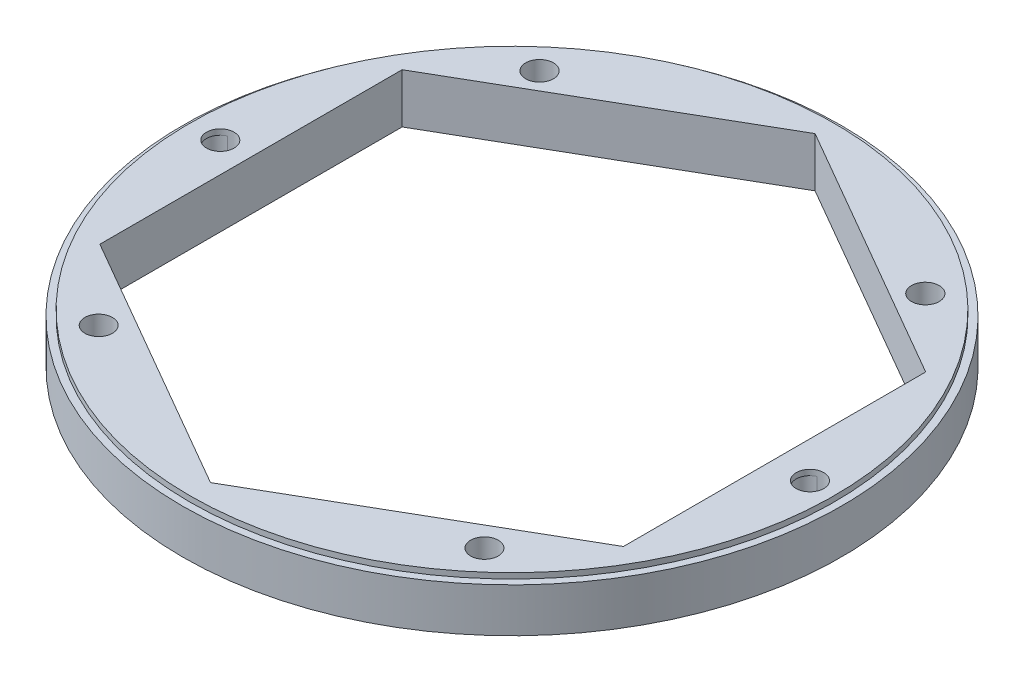
SolidWorks part; units mm, degrees
ref_plane "Front Plane" through (0, 0, 0) normal (0, 0, 1) x (1, 0, 0)
ref_plane "Top Plane" through (0, 0, 0) normal (0, 1, 0) x (1, 0, 0)
ref_plane "Right Plane" through (0, 0, 0) normal (1, 0, 0) x (0, 0, -1)
sketch "Sketch1" plane through (0, 0, 0) normal (0, 1, 0) x (1, 0, 0)
  circle A0 centre (0, 0) radius 75.946
  dimension "D1" = 151.892
extrude "Boss-Extrude1" add sketch "Sketch1" along normal blind 10.16
sketch "Sketch2" plane through (0, 10.16, 0) normal (0, 1, 0) x (1, 0, 0)
  line L0 (0, 63.5) -> (-52.8538, -35.1955)
  line L1 (-52.8538, -35.1955) -> (52.8538, -35.1955)
  line L2 (52.8538, -35.1955) -> (0, 63.5)
  circle A0 centre (0, 0) radius 75.946 construction
  dimension "D1" = 63.5
  dimension "D2" = 63.5
  dimension "D3" = 63.5
extrude "Cut-Extrude1" [suppressed] cut sketch "Sketch2" against normal blind 20.32
fillet "Fillet1" [suppressed] radius 2.54
sketch "Sketch3" [suppressed] plane through (0, 10.16, 0) normal (0, 1, 0) x (1, 0, 0)
  line L1 (33.8032, -46.5261) -> (54.6948, 17.7714)
  line L2 (54.6948, 17.7714) -> (0, 57.5095)
  line L3 (0, 57.5095) -> (-54.6948, 17.7714)
  line L4 (-54.6948, 17.7714) -> (-33.8032, -46.5261)
  line L5 (-33.8032, -46.5261) -> (33.8032, -46.5261)
  circle A0 centre (0, 0) radius 46.5261 construction
extrude "Cut-Extrude2" [suppressed] cut sketch "Sketch3" against normal blind 20.32
fillet "Fillet2" [suppressed] radius 2.54
sketch "Sketch4" [suppressed] plane through (0, 10.16, 0) normal (0, 1, 0) x (1, 0, 0)
  line L0 (0, 75.946) -> (0, -75.946) construction
  circle A0 centre (0, 0) radius 75.946 construction
  circle A1 centre (-23.8719, 55.6861) radius 3.175
  circle A2 centre (-50, -20.5139) radius 3.175
  circle A3 centre (23.8719, 55.6861) radius 3.175
  circle A4 centre (50, -20.5139) radius 3.175
  arc A5 (-53.2018, 18.8561) -> (-54.1245, 16.0163) centre (-51.7088, 16.8012) ccw construction
  point P16 (-54.1245, 17.5861)
  dimension "D1" = 6.35
  dimension "D2" = 6.35
  dimension "D3" = 76.2
  dimension "D4" = 38.1
  dimension "D5" = 100
extrude "Cut-Extrude3" [suppressed] cut sketch "Sketch4" against normal blind 20.32
sketch "Sketch5" plane through (0, 10.16, 0) normal (0, 1, 0) x (1, 0, 0)
  line L1 (0, 69.6573) -> (-60.325, 34.8287)
  line L2 (-60.325, 34.8287) -> (-60.325, -34.8287)
  line L3 (-60.325, -34.8287) -> (0, -69.6573)
  line L4 (0, -69.6573) -> (60.325, -34.8287)
  line L5 (60.325, -34.8287) -> (60.325, 34.8287)
  line L6 (60.325, 34.8287) -> (0, 69.6573)
  circle A0 centre (0, 0) radius 60.325 construction
  dimension "D1" = 120.65
extrude "Cut-Extrude4" cut sketch "Sketch5" against normal through all
fillet "Fillet3" [suppressed] radius 10
sketch "Sketch6" plane through (0, 10.16, 0) normal (0, 1, 0) x (1, 0, 0)
  line L0 (0, 75.946) -> (0, -75.946) construction
  line L1 (-75.946, 0) -> (75.946, 0) construction
  line L2 (-37.8426, 65.8463) -> (38.1032, -65.6958) construction
  line L3 (-37.973, -65.7712) -> (37.973, 65.7712) construction
  line L6 (-60.325, 34.8287) -> (-60.325, -34.8287) construction
  circle A0 centre (0, 0) radius 75.946 construction
  circle A1 centre (-67.945, 0) radius 3.1835
  circle A2 centre (-33.7796, 58.8089) radius 3.2
  circle A3 centre (-33.9533, -58.8089) radius 3.175
  circle A4 centre (33.9533, -58.8089) radius 3.175
  circle A5 centre (67.945, 0) radius 3.1835
  circle A6 centre (33.7796, 58.8089) radius 3.2
  dimension "D1" = 6.4
  dimension "D2" = 6.35
  dimension "D3" = 34.1654
  dimension "D4" = 7.62
extrude "Cut-Extrude5" cut sketch "Sketch6" against normal through all both and the other way through all
sketch "Sketch7" plane through (0, 10.16, 0) normal (0, 1, 0) x (1, 0, 0)
  circle A0 centre (0, 0) radius 74.295
  dimension "D1" = 148.59
extrude "Boss-Extrude2" add sketch "Sketch7" along normal blind 1.27
sketch "Sketch8" plane through (0, 11.43, 0) normal (0, 1, 0) x (1, 0, 0)
  line L0 (-75.946, 0) -> (75.946, 0) construction
  line L1 (0, 75.946) -> (0, -75.946) construction
  circle A0 centre (-67.4025, 0.1808) radius 3.1835
  circle A1 centre (-44.45, 50.8) radius 3.2
  circle A2 centre (-44.45, -50.8) radius 3.175
  circle A3 centre (44.45, -50.8) radius 3.175
  circle A4 centre (68.4875, 0.1808) radius 3.1835
  circle A5 centre (44.45, 50.8) radius 3.2
  circle A7 centre (0, 0) radius 75.946 construction
  dimension "D1" = 44.45
  dimension "D2" = 44.45
  dimension "D3" = 44.45
  dimension "D4" = 44.45
  dimension "D5" = 50.8
  dimension "D6" = 50.8
  dimension "D8" = 50.8
  dimension "D7" = 50.8
extrude "Cut-Extrude6" cut sketch "Sketch8" against normal through all
sketch "Sketch9" plane through (0, 11.43, 0) normal (0, 1, 0) x (1, 0, 0)
  line L0 (-0.1808, 70.019) -> (-60.5058, 35.1903)
  line L1 (-60.5058, 35.1903) -> (-60.5058, -34.467)
  line L2 (-60.5058, -34.467) -> (-0.1808, -69.2956)
  line L3 (-0.1808, -69.2956) -> (60.1442, -34.467)
  line L4 (60.1442, -34.467) -> (60.1442, 35.1903)
  line L5 (60.1442, 35.1903) -> (-0.1808, 70.019)
  circle A0 centre (-0.1808, 0.3617) radius 60.325 construction
extrude "Cut-Extrude7" cut sketch "Sketch9" against normal through all
